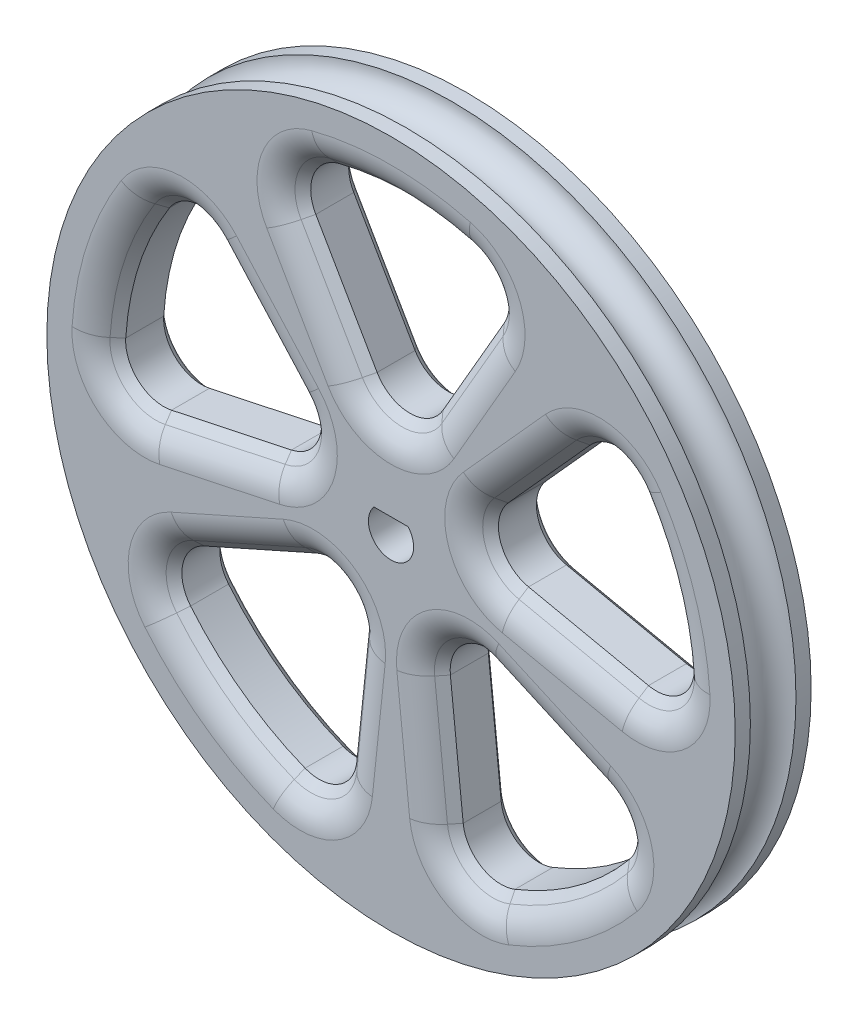
SolidWorks part; units mm, degrees
ref_plane "Front Plane" through (0, 0, 0) normal (0, 0, 1) x (1, 0, 0)
ref_plane "Top Plane" through (0, 0, 0) normal (0, 1, 0) x (1, 0, 0)
ref_plane "Right Plane" through (0, 0, 0) normal (1, 0, 0) x (0, 0, -1)
sketch "Sketch1" plane through (0, 0, 0) normal (0, 0, 1) x (1, 0, 0)
  circle A0 centre (0, 0) radius 23.0188
  dimension "D1" = 46.0375
extrude "Boss-Extrude1" add sketch "Sketch1" along normal blind 5.08
sketch "Sketch2" plane through (0, 0, 5.08) normal (0, 0, 1) x (1, 0, 0)
  line L0 (0, 0) -> (0, 19.05) construction
  line L1 (0, 3.81) -> (7.8275, 17.3676)
  line L2 (0, 3.81) -> (-7.8275, 17.3676)
  circle A0 centre (0, 0) radius 19.05 construction
  arc A1 (7.8275, 17.3676) -> (-7.8275, 17.3676) centre (0, 0) ccw
  dimension "D1" = 38.1
  dimension "D2" = 30
  dimension "D3" = 3.81
extrude "Cut-Extrude3" cut sketch "Sketch2" against normal up to surface (5.08 mm away) contours L1 A1 L2 up to face at (23.0188, 0, 0)
sketch3d "3DSketch1"
  line L0 (0, 0, 0) -> (0, 0, -15.5366) construction
fillet "Fillet3" radius 2.54 3 edges at (0, 3.81, 2.54) (-7.8275, 17.3676, 2.54) (7.8275, 17.3676, 2.54)
chamfer "Chamfer2" distance 1.27 angle 45 12 edges at (6.4421, 16.9773, 5.08) (4.2501, 11.1713, 5.08) (0, 6.35, 5.08) (-4.2501, 11.1713, 5.08) (0, 19.05, 5.08) (-6.4421, 16.9773, 5.08) (6.4421, 16.9773, 0) (4.2501, 11.1713, 0) (0, 6.35, 0) (-4.2501, 11.1713, 0) (-6.4421, 16.9773, 0) (0, 19.05, 0)
pattern_circular "CirPattern3" count 5 every 72 about axis through (0, 0, 0) along (0, 0, 1) of "Chamfer2", "Cut-Extrude3", "Fillet3"
sketch "Sketch5" plane through (0, 0, 5.08) normal (0, 0, 1) x (1, 0, 0)
  line L0 (-1.1414, 0.9906) -> (1.1414, 0.9906)
  circle A0 centre (0, 0) radius 1.5113 construction
  arc A1 (1.1414, 0.9906) -> (-1.1414, 0.9906) centre (0, 0) cw
  point P5 (0, -1.5113)
  dimension "D1" = 3.0226
  dimension "D2" = 2.5019
extrude "Cut-Extrude4" cut sketch "Sketch5" against normal up to surface (5.08 mm away) contours A1 L0 up to face at (12.9046, 4.1929, 0)
fillet "Fillet4" radius 2.54 60 edges at (-7.6128, 17.4696, 5.08) (-5.3499, 10.5363, 5.08) (0, 5.08, 5.08) (5.3499, 10.5363, 5.08) (7.6128, 17.4696, 5.08) (0, 20.32, 5.08) (-1.8649, -11.6687, 5.08) (-2.9859, -4.1098, 5.08) (-10.5213, -5.3795, 5.08) (-16.4273, -9.6586, 5.08) (-11.9438, -16.4392, 5.08) (-14.2621, 12.6386, 5.08) (-19.3255, 6.2792, 5.08) (-18.9671, -1.8418, 5.08) (-11.6738, -1.8322, 5.08) (-4.8314, 1.5698, 5.08) (-2.9859, -4.1098, 0) (-1.8649, -11.6687, 0) (-4.1095, -18.6079, 0) (-11.9438, -16.4392, 0) (-16.4273, -9.6586, 0) (-8.3674, 8.344, 0) (-4.8314, 1.5698, 0) (-11.6738, -1.8322, 0) (-18.9671, -1.8418, 0) (-19.3255, 6.2792, 0) (0, 20.32, 0) (7.6128, 17.4696, 0) (5.3499, 10.5363, 0) (0, 5.08, 0) (-5.3499, 10.5363, 0) (-4.1095, -18.6079, 5.08) (-8.3674, 8.344, 5.08) (-10.5213, -5.3795, 0) (-14.2621, 12.6386, 0) (-7.6128, 17.4696, 0) (16.4273, -9.6586, 0) (11.9438, -16.4392, 0) (4.1095, -18.6079, 0) (1.8649, -11.6687, 0) (2.9859, -4.1098, 0) (8.3674, 8.344, 0) (14.2621, 12.6386, 0) (19.3255, 6.2792, 0) (18.9671, -1.8418, 0) (11.6738, -1.8322, 0) (1.8649, -11.6687, 5.08) (4.1095, -18.6079, 5.08) (11.9438, -16.4392, 5.08) (16.4273, -9.6586, 5.08) (10.5213, -5.3795, 5.08) (4.8314, 1.5698, 5.08) (11.6738, -1.8322, 5.08) (18.9671, -1.8418, 5.08) (19.3255, 6.2792, 5.08) (14.2621, 12.6386, 5.08) (10.5213, -5.3795, 0) (4.8314, 1.5698, 0) (2.9859, -4.1098, 5.08) (8.3674, 8.344, 5.08)
sketch "Sketch7" plane through (0, 0, 0) normal (0, 1, 0) x (1, 0, 0)
  line L0 (-23.0188, 0) -> (-23.0188, -5.08) construction
  line L1 (-23.0188, -4.064) -> (-23.0188, -1.016)
  circle A0 centre (-23.0188, -2.54) radius 1.524 construction
  arc A1 (-23.0188, -1.016) -> (-23.0188, -4.064) centre (-23.0188, -2.54) cw
  dimension "D1" = 3.048
revolve "Cut-Revolve1" cut sketch "Sketch7" angle 360 about L0
